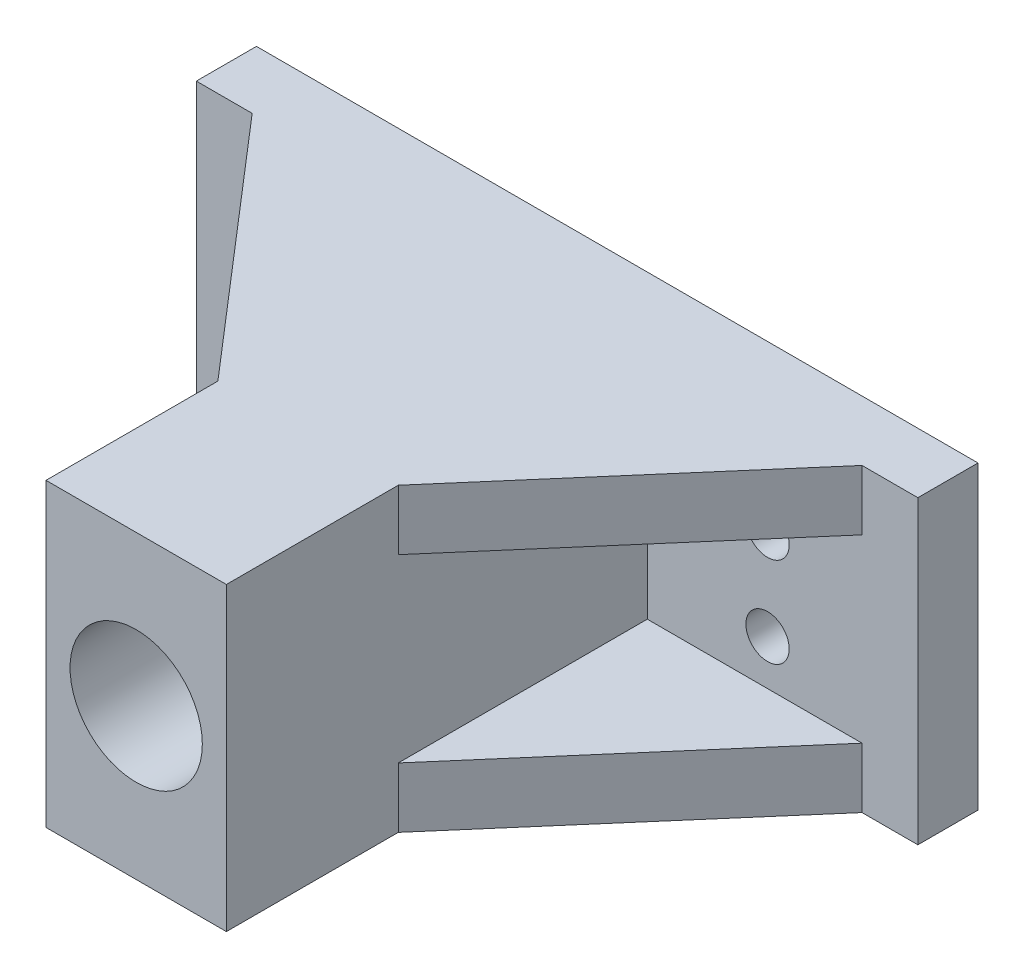
SolidWorks part; units mm, degrees
ref_plane "前视基准面" through (0, 0, 0) normal (0, 0, 1) x (1, 0, 0)
ref_plane "上视基准面" through (0, 0, 0) normal (0, 1, 0) x (1, 0, 0)
ref_plane "右视基准面" through (0, 0, 0) normal (1, 0, 0) x (0, 0, -1)
sketch "草图1" plane through (0, 0, 0) normal (0, 0, 1) x (1, 0, 0)
  line L1 (20, -7.5) -> (-20, -7.5)
  line L2 (20, -7.5) -> (20, 7.5)
  line L3 (20, 7.5) -> (-20, 7.5)
  line L4 (-20, -7.5) -> (-20, 7.5)
  line L5 (0, 7.5) -> (0, -7.5) construction
  line L6 (20, 0) -> (-20, 0) construction
  point P0 (0, 0)
  dimension "D1" = 15
  dimension "D2" = 40
extrude "凸台-拉伸1" add sketch "草图1" along normal blind 5
sketch "草图2" plane through (0, 0, 5) normal (0, 0, 1) x (1, 0, 0)
  line L0 (0, 0) -> (0, 16.7809) construction
  circle A0 centre (0, 0) radius 5.5
  circle A1 centre (-12, 0) radius 1.8
  circle A2 centre (12, 0) radius 1.8
  dimension "D1" = 11
  dimension "D2" = 3.6
  dimension "D3" = 12
extrude "切除-拉伸1" cut sketch "草图2" against normal blind 5
sketch "草图3" plane through (0, 0, 5) normal (0, 0, 1) x (1, 0, 0)
  line L0 (-7.5, 7.5) -> (-7.5, -7.5)
  line L1 (20, 7.5) -> (-20, 7.5) construction
  line L2 (-20, -7.5) -> (20, -7.5) construction
  line L3 (0, 7.5) -> (0, -7.5) construction
  line L4 (7.5, 7.5) -> (7.5, -7.5)
  line L5 (-7.5, 7.5) -> (7.5, 7.5)
  line L6 (-7.5, -7.5) -> (7.5, -7.5)
  circle A0 centre (0, 0) radius 5.05
  dimension "D1" = 15
extrude "凸台-拉伸2" add sketch "草图3" along normal blind 25
sketch "草图4" plane through (0, 0, 5) normal (0, 0, -1) x (-1, 0, 0)
  circle A0 centre (0, 0) radius 5.5
extrude "切除-拉伸2" cut sketch "草图4" against normal blind 31
sketch "草图5" plane through (0, 0, 5) normal (0, 0, 1) x (1, 0, 0)
  line L0 (-20, 7.5) -> (-30, 7.5)
  line L1 (-30, 7.5) -> (-30, -7.5)
  line L2 (-30, -7.5) -> (-20, -7.5)
  line L3 (-20, -7.5) -> (-20, 7.5)
  line L4 (0, 7.5) -> (0, -7.5) construction
  line L5 (7.5, 7.5) -> (-7.5, 7.5) construction
  line L6 (-7.5, -7.5) -> (7.5, -7.5) construction
  line L7 (30, -7.5) -> (20, -7.5)
  line L8 (20, -7.5) -> (20, 7.5)
  line L9 (20, 7.5) -> (30, 7.5)
  line L10 (30, 7.5) -> (30, -7.5)
  dimension "D1" = 10
extrude "凸台-拉伸3" add sketch "草图5" against normal blind 5
sketch "草图6" plane through (0, 0, 5) normal (0, 0, 1) x (1, 0, 0)
  line L0 (0, 0) -> (0, 14.0477) construction
  circle A0 centre (-24, 0) radius 1.8
  circle A1 centre (24, 0) radius 1.8
  circle A2 centre (-12, 0) radius 1.8 construction
  dimension "D1" = 3.6
  dimension "D2" = 12
extrude "切除-拉伸3" cut sketch "草图6" against normal blind 5
sketch "草图7" plane through (0, 0, 5) normal (0, 0, 1) x (1, 0, 0)
  line L0 (-30, 7.5) -> (-30, 12.5)
  line L1 (-30, 12.5) -> (30, 12.5)
  line L2 (30, 12.5) -> (30, 7.5)
  line L3 (30, 7.5) -> (-30, 7.5)
  line L4 (0, 0) -> (-30, 0) construction
  line L5 (-30, 7.5) -> (-30, -7.5) construction
  line L6 (-30, -12.5) -> (30, -12.5)
  line L7 (30, -12.5) -> (30, -7.5)
  line L8 (30, -7.5) -> (-30, -7.5)
  line L9 (-30, -7.5) -> (-30, -12.5)
  dimension "D1" = 5
extrude "凸台-拉伸4" add sketch "草图7" against normal blind 5
sketch "草图8" plane through (0, 0, 5) normal (0, 0, 1) x (1, 0, 0)
  line L0 (-7.5, 7.5) -> (-7.5, 12.5)
  line L1 (30, 12.5) -> (-30, 12.5) construction
  line L2 (-7.5, 12.5) -> (7.5, 12.5)
  line L3 (7.5, 12.5) -> (7.5, 7.5)
  line L4 (7.5, 7.5) -> (-7.5, 7.5)
  line L5 (-7.5, -7.5) -> (-7.5, -12.5)
  line L6 (-30, -12.5) -> (30, -12.5) construction
  line L7 (-7.5, -12.5) -> (7.5, -12.5)
  line L8 (7.5, -12.5) -> (7.5, -7.5)
  line L9 (7.5, -7.5) -> (-7.5, -7.5)
extrude "凸台-拉伸5" add sketch "草图8" along normal up to surface (25 mm away) up to face at (-5.5, 0, 30)
sketch "草图9" plane through (0, 12.5, 0) normal (0, 1, 0) x (1, 0, 0)
  line L0 (-25.3552, -5) -> (-7.5, -25.7076)
  line L1 (-7.5, -5) -> (-30, -5) construction
  line L2 (-7.5, -30) -> (-7.5, -5) construction
rib "筋1" sketch "草图9" sketch "草图9" thickness 5 extrusion direction parallel to sketch draft on no parameters "D1"=5
ref_plane "基准面1" through (0, 0, 0) normal (0, 1, 0) x (1, 0, 0)
mirror "镜向1" about plane through (0, 0, 0) normal (0, 1, 0) of "筋1"
ref_plane "基准面3" through (0, 0, 0) normal (-1, 0, 0) x (0, 0, 1)
mirror "镜向2" about plane through (0, 0, 0) normal (-1, 0, 0) of "镜向1", "筋1"
sketch "草图11" plane through (0, 0, 5) normal (0, 0, 1) x (1, 0, 0)
  circle A0 centre (-24, 0) radius 1.8
  circle A1 centre (-12, 0) radius 1.8
  circle A2 centre (12, 0) radius 1.8
  circle A3 centre (24, 0) radius 1.8
extrude "凸台-拉伸6" add sketch "草图11" against normal blind 5
sketch "草图12" plane through (0, 0, 5) normal (0, 0, 1) x (1, 0, 0)
  line L0 (0, 0) -> (-41.3935, 0) construction
  line L1 (-7.5, 7.5) -> (-7.5, 0) construction
  line L2 (-7.5, 12.5) -> (-7.5, -12.5) construction
  line L3 (0, 0) -> (0, 26.5844) construction
  circle A0 centre (-17.5, 3.75) radius 1.8
  circle A1 centre (-17.5, -3.75) radius 1.8
  circle A2 centre (17.5, -3.75) radius 1.8
  circle A3 centre (17.5, 3.75) radius 1.8
  point P10 (-7.5, 3.75)
  dimension "D1" = 3.6
  dimension "D2" = 10
extrude "切除-拉伸4" cut sketch "草图12" against normal blind 5
sketch "草图13" plane through (0, 0, 30) normal (0, 0, 1) x (1, 0, 0)
  line L0 (-7.5, 12.5) -> (-7.5, -12.5)
  line L1 (-7.5, -12.5) -> (7.5, -12.5)
  line L2 (7.5, -12.5) -> (7.5, 12.5)
  line L3 (7.5, 12.5) -> (-7.5, 12.5)
  circle A0 centre (0, 0) radius 5.5
extrude "凸台-拉伸7" add sketch "草图13" along normal blind 10
